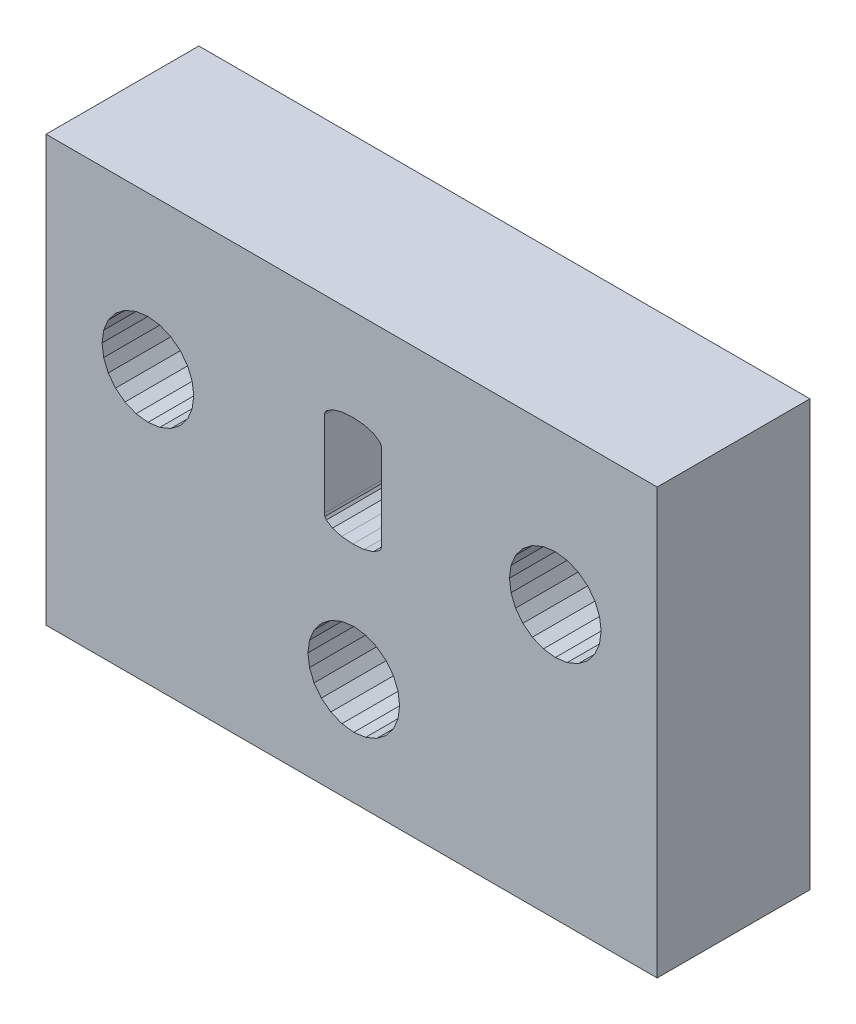
SolidWorks part; units mm, degrees
material "Maple"
ref_plane "Front Plane" through (0, 0, 0) normal (0, 0, 1) x (1, 0, 0)
ref_plane "Top Plane" through (0, 0, 0) normal (0, 1, 0) x (1, 0, 0)
ref_plane "Right Plane" through (0, 0, 0) normal (1, 0, 0) x (0, 0, -1)
sketch "Sketch1" plane through (0, 0, 0) normal (0, 0, 1) x (1, 0, 0)
  line L7008 (240.6989, 115.982) -> (264.6989, 115.982)
  line L7009 (246.4376, 109.5161) -> (246.4989, 109.982)
  line L7010 (240.6989, 99.282) -> (240.6989, 115.982)
  line L7011 (258.9591, 109.5161) -> (259.1389, 109.082)
  line L7012 (243.7989, 108.4232) -> (244.233, 108.2434)
  line L7013 (246.4989, 109.982) -> (246.4376, 110.4479)
  line L7014 (262.4978, 109.982) -> (262.4364, 110.4479)
  line L7015 (261.9706, 111.2548) -> (261.5978, 111.5409)
  line L7016 (264.6989, 115.982) -> (264.6989, 99.282)
  line L7017 (246.2577, 109.082) -> (246.4376, 109.5161)
  line L7018 (243.14, 110.882) -> (242.9602, 110.4479)
  line L7019 (246.2577, 110.882) -> (245.9717, 111.2548)
  line L7020 (259.7978, 108.4232) -> (260.2319, 108.2434)
  line L7021 (264.6989, 99.282) -> (240.6989, 99.282)
  line L7022 (251.045, 103.9479) -> (250.9836, 103.482)
  line L7023 (250.9836, 103.482) -> (251.045, 103.0161)
  line L7024 (242.8989, 109.982) -> (242.9602, 109.5161)
  line L7025 (253.2495, 101.7434) -> (253.6836, 101.9232)
  line L7026 (262.4364, 110.4479) -> (262.2566, 110.882)
  line L7027 (251.2248, 102.582) -> (251.5109, 102.2092)
  line L7028 (244.233, 108.2434) -> (244.6989, 108.182)
  line L7029 (251.2248, 104.382) -> (251.045, 103.9479)
  line L7030 (251.8836, 105.0409) -> (251.5109, 104.7548)
  line L7031 (254.3425, 104.382) -> (254.0564, 104.7548)
  line L7032 (254.0564, 102.2092) -> (254.3425, 102.582)
  line L7033 (261.9706, 108.7092) -> (262.2566, 109.082)
  line L7034 (254.5223, 103.0161) -> (254.5836, 103.482)
  line L7035 (261.5978, 108.4232) -> (261.9706, 108.7092)
  line L7036 (259.425, 108.7092) -> (259.7978, 108.4232)
  line L7037 (260.6978, 111.782) -> (260.2319, 111.7207)
  line L7038 (244.6989, 108.182) -> (245.1648, 108.2434)
  line L7039 (254.5836, 103.482) -> (254.5223, 103.9479)
  line L7040 (259.1389, 109.082) -> (259.425, 108.7092)
  line L7041 (254.3425, 102.582) -> (254.5223, 103.0161)
  line L7042 (243.7989, 111.5409) -> (243.4261, 111.2548)
  line L7043 (261.5978, 111.5409) -> (261.1636, 111.7207)
  line L7044 (260.2319, 108.2434) -> (260.6978, 108.182)
  line L7045 (253.6836, 101.9232) -> (254.0564, 102.2092)
  line L7046 (245.1648, 108.2434) -> (245.5989, 108.4232)
  line L7047 (242.9602, 109.5161) -> (243.14, 109.082)
  line L7048 (262.4364, 109.5161) -> (262.4978, 109.982)
  line L7049 (254.5223, 103.9479) -> (254.3425, 104.382)
  line L7050 (252.3178, 101.7434) -> (252.7836, 101.682)
  line L7051 (243.4261, 108.7092) -> (243.7989, 108.4232)
  line L7052 (245.5989, 111.5409) -> (245.1648, 111.7207)
  line L7053 (259.1389, 110.882) -> (258.9591, 110.4479)
  line L7054 (258.9591, 110.4479) -> (258.8978, 109.982)
  line L7055 (245.9717, 108.7092) -> (246.2577, 109.082)
  line L7056 (243.14, 109.082) -> (243.4261, 108.7092)
  line L7057 (258.8978, 109.982) -> (258.9591, 109.5161)
  line L7058 (252.3178, 105.2207) -> (251.8836, 105.0409)
  line L7059 (260.6978, 108.182) -> (261.1636, 108.2434)
  line L7060 (244.6989, 111.782) -> (244.233, 111.7207)
  line L7061 (259.7978, 111.5409) -> (259.425, 111.2548)
  line L7062 (251.8836, 101.9232) -> (252.3178, 101.7434)
  line L7063 (259.425, 111.2548) -> (259.1389, 110.882)
  line L7064 (260.2319, 111.7207) -> (259.7978, 111.5409)
  line L7065 (251.045, 103.0161) -> (251.2248, 102.582)
  line L7066 (252.7836, 101.682) -> (253.2495, 101.7434)
  line L7067 (245.5989, 108.4232) -> (245.9717, 108.7092)
  line L7068 (242.9602, 110.4479) -> (242.8989, 109.982)
  line L7069 (243.4261, 111.2548) -> (243.14, 110.882)
  line L7070 (244.233, 111.7207) -> (243.7989, 111.5409)
  line L7071 (245.1648, 111.7207) -> (244.6989, 111.782)
  line L7072 (245.9717, 111.2548) -> (245.5989, 111.5409)
  line L7073 (246.4376, 110.4479) -> (246.2577, 110.882)
  line L7074 (261.1636, 111.7207) -> (260.6978, 111.782)
  line L7075 (262.2566, 110.882) -> (261.9706, 111.2548)
  line L7076 (262.2566, 109.082) -> (262.4364, 109.5161)
  line L7077 (261.1636, 108.2434) -> (261.5978, 108.4232)
  line L7078 (251.5109, 104.7548) -> (251.2248, 104.382)
  line L7079 (252.7836, 105.282) -> (252.3178, 105.2207)
  line L7080 (253.2495, 105.2207) -> (252.7836, 105.282)
  line L7081 (253.6836, 105.0409) -> (253.2495, 105.2207)
  line L7082 (254.0564, 104.7548) -> (253.6836, 105.0409)
  line L7083 (251.5109, 102.2092) -> (251.8836, 101.9232)
  line L9478 (251.6265, 108.5493) -> (251.6466, 108.4531)
  line L9479 (251.6466, 108.4531) -> (251.7069, 108.3643)
  line L9480 (251.7069, 108.3643) -> (251.9481, 108.209)
  line L9481 (251.9481, 108.209) -> (252.3094, 108.1037)
  line L9482 (252.3094, 108.1037) -> (252.7504, 108.0685)
  line L9483 (252.7504, 108.0685) -> (253.1914, 108.1037)
  line L9484 (253.1914, 108.1037) -> (253.5528, 108.209)
  line L9485 (253.5528, 108.209) -> (253.7939, 108.3643)
  line L9486 (253.7939, 108.3643) -> (253.8542, 108.4531)
  line L9487 (253.8542, 108.4531) -> (253.8743, 108.5493)
  line L9488 (253.8743, 108.5493) -> (253.8743, 111.8957)
  line L9489 (253.8743, 111.8957) -> (253.8542, 111.9919)
  line L9490 (253.8542, 111.9919) -> (253.7939, 112.0807)
  line L9491 (253.7939, 112.0807) -> (253.5528, 112.236)
  line L9492 (253.5528, 112.236) -> (253.1914, 112.3413)
  line L9493 (253.1914, 112.3413) -> (252.7504, 112.3765)
  line L9494 (252.7504, 112.3765) -> (252.3094, 112.3413)
  line L9495 (252.3094, 112.3413) -> (251.9481, 112.236)
  line L9496 (251.9481, 112.236) -> (251.7069, 112.0807)
  line L9497 (251.7069, 112.0807) -> (251.6466, 111.9919)
  line L9498 (251.6466, 111.9919) -> (251.6265, 111.8957)
  line L9499 (251.6265, 111.8957) -> (251.6265, 108.5493)
  line L9500 (253.8743, 108.5493) -> (253.8542, 108.4531)
  line L9501 (253.8542, 108.4531) -> (253.7939, 108.3643)
  line L9502 (253.7939, 108.3643) -> (253.5528, 108.209)
  line L9503 (253.5528, 108.209) -> (253.1914, 108.1037)
  line L9504 (253.1914, 108.1037) -> (252.7504, 108.0685)
  line L9505 (252.7504, 108.0685) -> (252.3094, 108.1037)
  line L9506 (252.3094, 108.1037) -> (251.9481, 108.209)
  line L9507 (251.9481, 108.209) -> (251.7069, 108.3643)
  line L9508 (251.7069, 108.3643) -> (251.6466, 108.4531)
  line L9509 (251.6466, 108.4531) -> (251.6265, 108.5493)
  line L9510 (251.6265, 108.5493) -> (251.6265, 111.8957)
  line L9511 (251.6265, 111.8957) -> (251.6466, 111.9919)
  line L9512 (251.6466, 111.9919) -> (251.7069, 112.0807)
  line L9513 (251.7069, 112.0807) -> (251.9481, 112.236)
  line L9514 (251.9481, 112.236) -> (252.3094, 112.3413)
  line L9515 (252.3094, 112.3413) -> (252.7504, 112.3765)
  line L9516 (252.7504, 112.3765) -> (253.1914, 112.3413)
  line L9517 (253.1914, 112.3413) -> (253.5528, 112.236)
  line L9518 (253.5528, 112.236) -> (253.7939, 112.0807)
  line L9519 (253.7939, 112.0807) -> (253.8542, 111.9919)
  line L9520 (253.8542, 111.9919) -> (253.8743, 111.8957)
  line L9521 (253.8743, 111.8957) -> (253.8743, 108.5493)
extrude "Boss-Extrude1" add sketch "Sketch1" along normal blind 6 contours L7021 L7016 L7008 L7010 L9499 L9498 L9497 L9496 L9495 L9494 L9493 L9492 L9491 L9490 L9489 L9488 L9487 L9486 L9485 L9484 L9483 L9482 L9481 L9480 L9479 L9478 L7083 L7027 L7065 L7023 L7022 L7029 L7078 L7030 L7058 L7079 L7080 L7081 L7082 L7031 L7049 L7039 L7034 L7041 L7032 L7045 L7025 L7066 L7050
